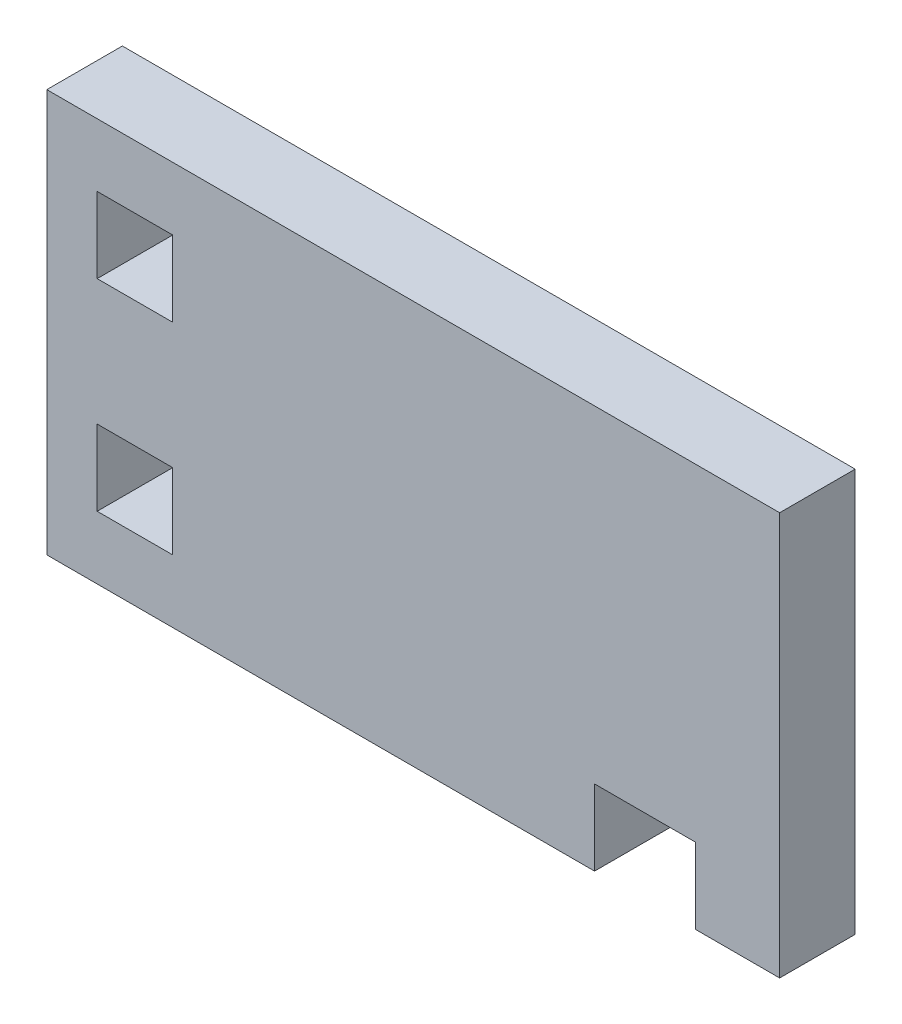
SolidWorks part; units mm, degrees
ref_plane "Front Plane" through (0, 0, 0) normal (0, 0, 1) x (1, 0, 0)
ref_plane "Top Plane" through (0, 0, 0) normal (0, 1, 0) x (1, 0, 0)
ref_plane "Right Plane" through (0, 0, 0) normal (1, 0, 0) x (0, 0, -1)
sketch "Sketch1" plane through (0, 0, 0) normal (0, 0, 1) x (1, 0, 0)
  line L0 (0, 0) -> (0, 80)
  line L1 (0, 80) -> (145.5, 80)
  line L2 (145.5, 80) -> (145.5, 0)
  line L3 (145.5, 0) -> (128.75, 0)
  line L4 (128.75, 0) -> (128.75, 15)
  line L5 (128.75, 15) -> (108.75, 15)
  line L6 (108.75, 15) -> (108.75, 0)
  line L7 (108.75, 0) -> (0, 0)
  line L9 (10, 67.5) -> (25, 67.5)
  line L10 (10, 67.5) -> (10, 52.5)
  line L11 (10, 52.5) -> (25, 52.5)
  line L12 (25, 67.5) -> (25, 52.5)
  line L13 (10, 27.5) -> (25, 27.5)
  line L14 (10, 27.5) -> (10, 12.5)
  line L15 (10, 12.5) -> (25, 12.5)
  line L16 (25, 27.5) -> (25, 12.5)
  dimension "D1" = 80
  dimension "D2" = 145.5
  dimension "D3" = 20
  dimension "D4" = 15
  dimension "D5" = 15
  dimension "D6" = 15
  dimension "D7" = 15
  dimension "D8" = 15
  dimension "D9" = 10
  dimension "D10" = 12.5
  dimension "D11" = 25
  dimension "D12" = 16.75
extrude "Boss-Extrude1" add sketch "Sketch1" along normal blind 15
